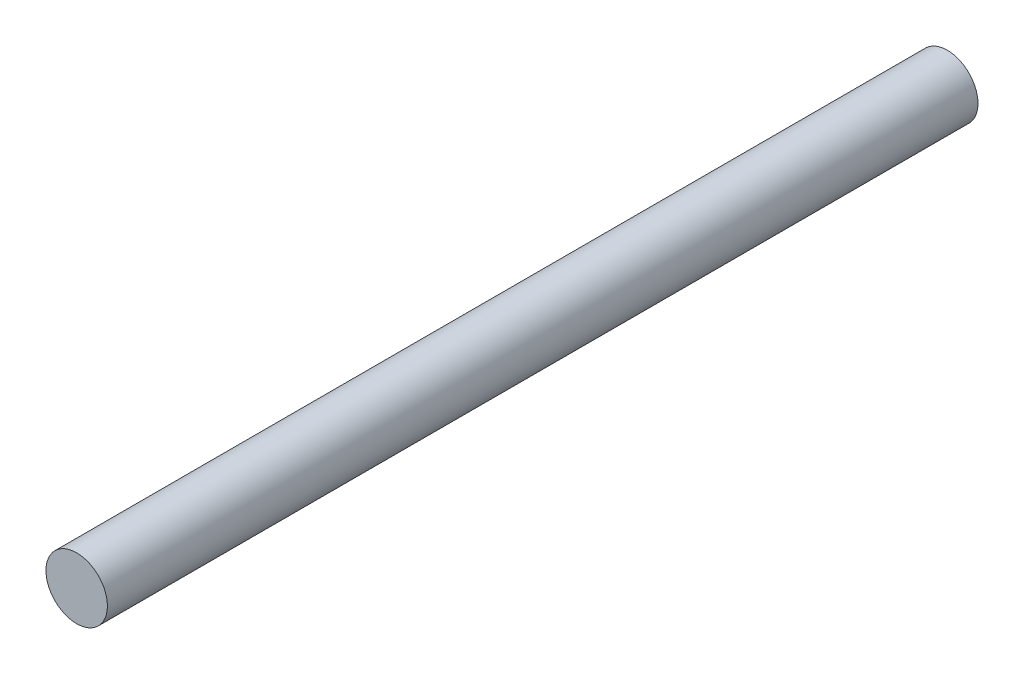
SolidWorks part; units mm, degrees
ref_plane "Alzado" through (0, 0, 0) normal (0, 0, 1) x (1, 0, 0)
ref_plane "Planta" through (0, 0, 0) normal (0, 1, 0) x (1, 0, 0)
ref_plane "Vista lateral" through (0, 0, 0) normal (1, 0, 0) x (0, 0, -1)
sketch "Croquis1" plane through (0, 0, 0) normal (0, 0, 1) x (1, 0, 0)
  circle A0 centre (0, 0) radius 6
  dimension "D1" = 12
extrude "Saliente-Extruir1" add sketch "Croquis1" along normal blind 170
